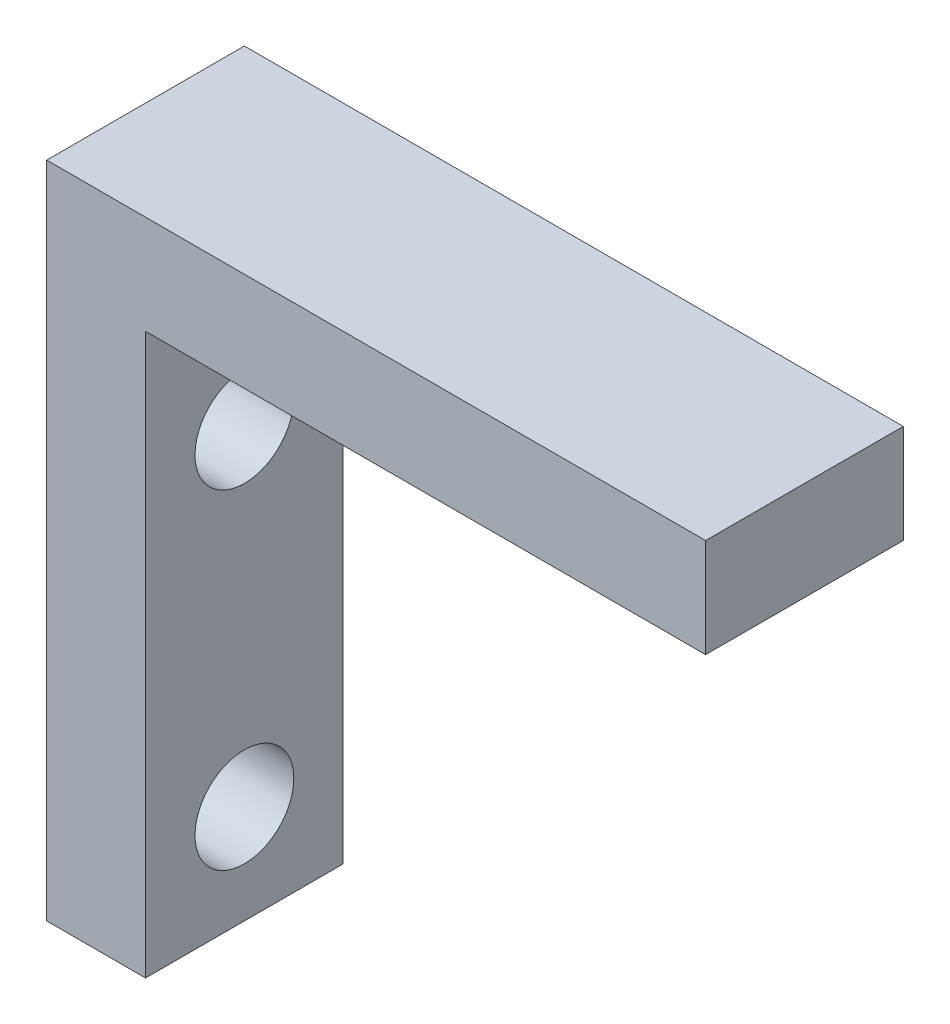
SolidWorks part; units mm, degrees
ref_plane "Front Plane" through (0, 0, 0) normal (0, 0, 1) x (1, 0, 0)
ref_plane "Top Plane" through (0, 0, 0) normal (0, 1, 0) x (1, 0, 0)
ref_plane "Right Plane" through (0, 0, 0) normal (1, 0, 0) x (0, 0, -1)
sketch "Sketch1" plane through (0, 0, 0) normal (0, 0, 1) x (1, 0, 0)
  line L0 (0, 0) -> (-20, 0)
  line L1 (-20, 0) -> (-20, -20)
  line L2 (-20, -20) -> (-17, -20)
  line L3 (-17, -20) -> (-17, -3)
  line L4 (-17, -3) -> (0, -3)
  line L5 (0, -3) -> (0, 0)
  dimension "D1" = 20
  dimension "D2" = 17
extrude "Boss-Extrude1" add sketch "Sketch1" along normal blind 6
sketch "Sketch4" plane through (-20, 0, 0) normal (-1, 0, 0) x (0, 0, 1)
  line L0 (6, 0) -> (0, 0) construction
  circle A0 centre (3, -7) radius 1.5
  circle A1 centre (3, -17) radius 1.5
  point P4 (0, 0)
  dimension "D1" = 7
  dimension "D2" = 10
extrude "Cut-Extrude1" cut sketch "Sketch4" against normal blind 3
